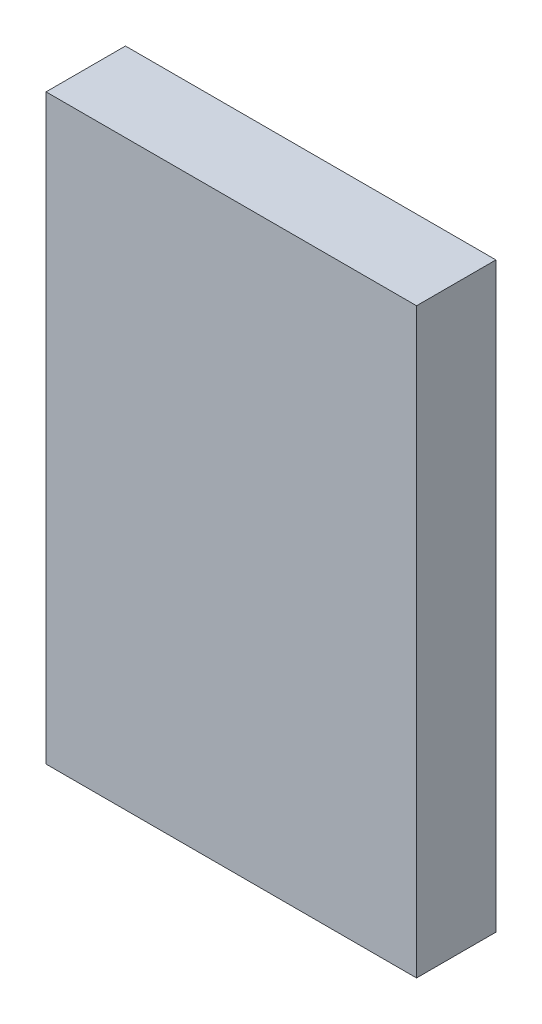
SolidWorks part; units mm, degrees
ref_plane "Front Plane" through (0, 0, 0) normal (0, 0, 1) x (1, 0, 0)
ref_plane "Top Plane" through (0, 0, 0) normal (0, 1, 0) x (1, 0, 0)
ref_plane "Right Plane" through (0, 0, 0) normal (1, 0, 0) x (0, 0, -1)
sketch "Sketch1" plane through (0, 0, 0) normal (0, 0, 1) x (1, 0, 0)
  line L1 (-23.0821, 9.906) -> (-2.0821, 9.906)
  line L2 (-23.0821, 9.906) -> (-23.0821, 42.906)
  line L3 (-23.0821, 42.906) -> (-2.0821, 42.906)
  line L4 (-2.0821, 9.906) -> (-2.0821, 42.906)
  line L5 (-2, 0) -> (-23.09, 0) construction
  line L6 (-10.259, 9.906) -> (-14.831, 9.906) construction
  line L7 (-2, 0) -> (-23.09, 0) construction
  line L8 (-10.259, 9.906) -> (-14.831, 9.906) construction
  line L9 (-12.545, 9.906) -> (-12.5821, 9.906) construction
  dimension "D1" = 21
  dimension "D2" = 33
extrude "Boss-Extrude1" add sketch "Sketch1" along normal blind 4.5 from offset 2
